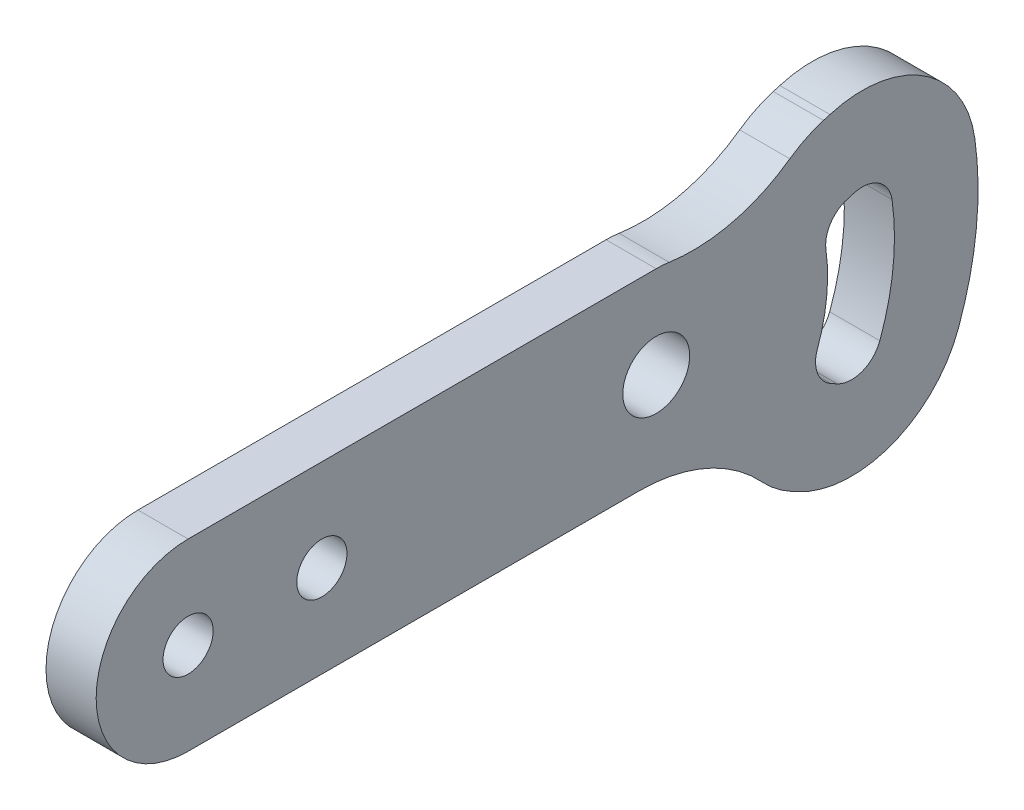
SolidWorks part; units mm, degrees
material "1060 Alloy"
ref_plane "Front Plane" through (0, 0, 0) normal (0, 0, 1) x (1, 0, 0)
ref_plane "Top Plane" through (0, 0, 0) normal (0, 1, 0) x (1, 0, 0)
ref_plane "Right Plane" through (0, 0, 0) normal (1, 0, 0) x (0, 0, -1)
sketch "Sketch1" plane through (0, 0, 0) normal (1, 0, 0) x (0, 0, -1)
  line L0 (0, 0) -> (28, 0) construction
  line L1 (355.5625, 23.1798) -> (355.5625, -448.1536) construction
  line L2 (0, 0) -> (28, 0) construction
  line L3 (0, 5.5) -> (28, 5.5)
  line L4 (0, -5.5) -> (28, -5.5)
  line L5 (28, 0) -> (32.8335, -2.6244)
  line L6 (28, 0) -> (33.2735, 1.5621)
  line L7 (28, 0) -> (42.1719, -1.4895) construction
  line L8 (28, 0) -> (42.25, 0) construction
  line L9 (39.4241, 3.384) -> (39.8119, 3.4988)
  line L10 (38.4709, -5.6853) -> (38.8263, -5.8782)
  line L11 (38.0041, 8.1781) -> (38.3918, 8.2929)
  line L12 (36.0851, -10.0793) -> (36.4405, -10.2723)
  circle A0 centre (0, 0) radius 1.5
  circle A1 centre (8, 0) radius 1.5
  circle A2 centre (28, 0) radius 2
  arc A3 (0, 5.5) -> (0, -5.5) centre (0, 0) ccw
  arc A4 (28, -5.5) -> (28, 5.5) centre (28, 0) ccw
  arc A8 (39.4241, 3.384) -> (38.1525, 1.4104) centre (39.9354, 1.6581) ccw
  arc A9 (39.8119, 3.4988) -> (42.1048, 2.0293) centre (40.3231, 1.773) cw
  arc A11 (41.3746, -4.9175) -> (42.1048, 2.0293) centre (28, 0) ccw
  arc A12 (38.7655, -5.8452) -> (39.7455, 3.4792) centre (28, 0) ccw
  arc A13 (37.6374, -3.4904) -> (38.1525, 1.4104) centre (28, 0) ccw
  arc A14 (37.6374, -3.4904) -> (38.4709, -5.6853) centre (39.3298, -4.1034) ccw
  arc A15 (38.8263, -5.8782) -> (41.3746, -4.9175) centre (39.6852, -4.2963) ccw
  arc A16 (36.4405, -10.2723) -> (46.0675, -6.6429) centre (39.6852, -4.2963) ccw
  arc A17 (46.0675, -6.6429) -> (47.0538, 2.7413) centre (28, 0) ccw
  arc A18 (38.3918, 8.2929) -> (47.0538, 2.7413) centre (40.3231, 1.773) cw
  arc A19 (38.0041, 8.1781) -> (33.2001, 0.7224) centre (39.9354, 1.6581) ccw
  arc A20 (32.9362, -1.7878) -> (33.2001, 0.7224) centre (28, 0) ccw
  arc A21 (32.9362, -1.7878) -> (36.0851, -10.0793) centre (39.3298, -4.1034) ccw
  point P8 (14, 0)
  point P26 (37.8279, 2.9112)
  point P35 (37.0079, -4.8909)
  dimension "D1" = 3
  dimension "D2" = 3
  dimension "D3" = 4
  dimension "D5" = 20
  dimension "D7" = 2
  dimension "D8" = 2
  dimension "D9" = 10.25
  dimension "D13" = 4
  dimension "D14" = 1.8
  dimension "D4" = 8
  dimension "D6" = 11
  dimension "D10" = 45
  dimension "D11" = 6
  dimension "D12" = 22.5
  dimension "D15" = 5
  dimension "D16" = 5
  dimension "D17" = 5
extrude "Boss-Extrude1" add sketch "Sketch1" along normal blind 3 contours A4 A21 L12 A16 A17 A18 L11 A19 A15 L10 A14 A13 A8 L9 A9 A11 | A1 | A0 | A2
fillet "Fillet1" radius 10 2 edges at (1.5, -2.9789, -32.6234) (1.5, 1.9525, -33.1418)
